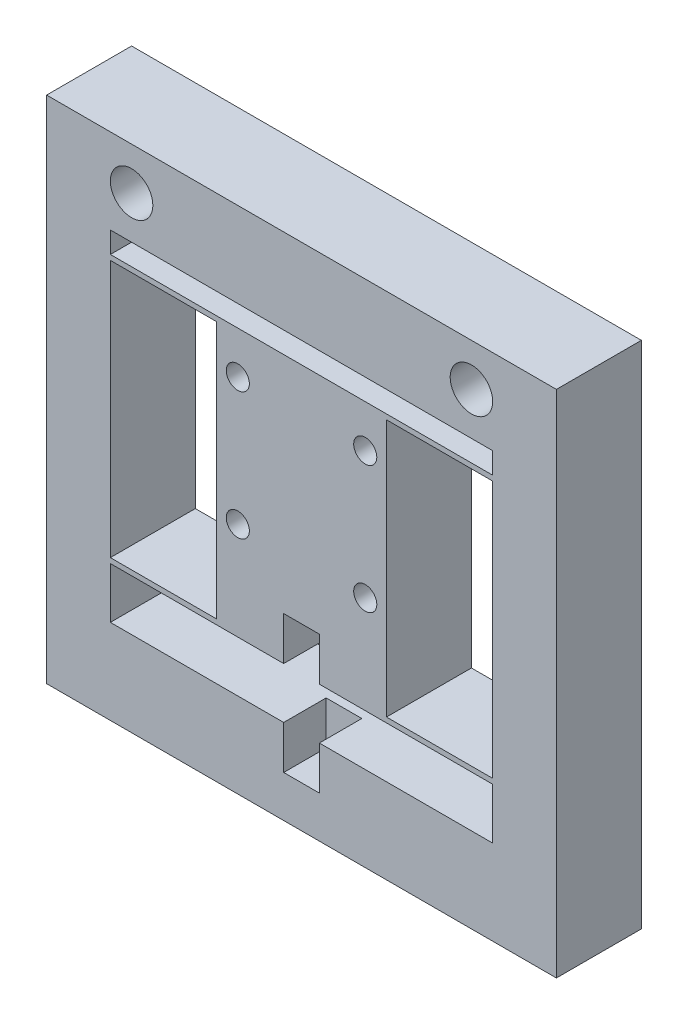
SolidWorks part; units mm, degrees
material "6061 Alloy"
ref_plane "Front Plane" through (0, 0, 0) normal (0, 0, 1) x (1, 0, 0)
ref_plane "Top Plane" through (0, 0, 0) normal (0, 1, 0) x (1, 0, 0)
ref_plane "Right Plane" through (0, 0, 0) normal (1, 0, 0) x (0, 0, -1)
sketch "Sketch1" plane through (0, 0, 0) normal (0, 0, 1) x (1, 0, 0)
  line L1 (-38.1, 38.1) -> (38.1, 38.1)
  line L2 (-38.1, 38.1) -> (-38.1, -38.1)
  line L3 (-38.1, -38.1) -> (38.1, -38.1)
  line L4 (38.1, 38.1) -> (38.1, -38.1)
  dimension "D1" = 38.1
  dimension "D2" = 38.1
  dimension "D3" = 38.1
  dimension "D4" = 38.1
extrude "Boss-Extrude1" add sketch "Sketch1" along normal mid plane 12.7
sketch "Sketch2" plane through (0, 0, 6.35) normal (0, 0, 1) x (1, 0, 0)
  line L0 (38.1, 38.1) -> (-38.1, 38.1) construction
  line L1 (-28.575, 25.4) -> (28.575, 25.4)
  line L2 (-28.575, 25.4) -> (-28.575, 22.225)
  line L3 (-28.575, 22.225) -> (28.575, 22.225)
  line L4 (28.575, 25.4) -> (28.575, 22.225)
  line L5 (12.7, 21.463) -> (28.575, 21.463)
  line L6 (12.7, 21.463) -> (12.7, -17.018)
  line L7 (12.7, -17.018) -> (28.575, -17.018)
  line L8 (28.575, 21.463) -> (28.575, -17.018)
  line L9 (-28.575, 21.463) -> (-12.7, 21.463)
  line L10 (-28.575, 21.463) -> (-28.575, -17.018)
  line L11 (-28.575, -17.018) -> (-12.7, -17.018)
  line L12 (-12.7, 21.463) -> (-12.7, -17.018)
  line L13 (-28.575, -17.78) -> (28.575, -17.78)
  line L14 (-28.575, -17.78) -> (-28.575, -25.4)
  line L15 (-28.575, -25.4) -> (28.575, -25.4)
  line L16 (28.575, -17.78) -> (28.575, -25.4)
  line L17 (38.1, -38.1) -> (38.1, 38.1) construction
  line L18 (-38.1, 38.1) -> (-38.1, -38.1) construction
  line L19 (-38.1, -38.1) -> (38.1, -38.1) construction
  dimension "D1" = 12.7
  dimension "D2" = 9.525
  dimension "D3" = 9.525
  dimension "D4" = 0.762
  dimension "D5" = 0.762
  dimension "D6" = 12.7
  dimension "D7" = 3.175
  dimension "D8" = 7.62
  dimension "D9" = 25.4
  dimension "D10" = 12.7
extrude "Cut-Extrude1" cut sketch "Sketch2" against normal through all
sketch "Sketch3" plane through (0, 0, 6.35) normal (0, 0, 1) x (1, 0, 0)
  line L0 (28.575, -17.78) -> (-28.575, -17.78) construction
  line L1 (-2.667, -11.303) -> (2.667, -11.303)
  line L2 (-2.667, -11.303) -> (-2.667, -31.877)
  line L3 (-2.667, -31.877) -> (2.667, -31.877)
  line L4 (2.667, -11.303) -> (2.667, -31.877)
  line L5 (-28.575, -25.4) -> (28.575, -25.4) construction
  dimension "D1" = 2.667
  dimension "D2" = 2.667
  dimension "D3" = 20.574
  dimension "D4" = 6.477
  dimension "D5" = 6.477
extrude "Cut-Extrude2" cut sketch "Sketch3" against normal blind 6.35
hole_wizard "1/4 (0.25) Diameter Hole1" positions "Sketch5" profile "Sketch4" hole size "1/4" standard "ANSI Inch" end condition up to next
sketch "Sketch5" plane through (0, 0, 6.35) normal (0, 0, 1) x (1, 0, 0)
  line L0 (38.1, 38.1) -> (-38.1, 38.1) construction
  point P0 (-25.4, 31.75)
  point P2 (25.4, 31.75)
  dimension "D1" = 25.4
  dimension "D2" = 25.4
  dimension "D3" = 6.35
sketch "Sketch4" plane through (-25.4, 31.75, 6.35) normal (1, 0, 0) x (0, -1, 0)
  line L0 (0, 0) -> (0, 12.7)
  line L1 (0, 12.7) -> (3.175, 12.7)
  line L2 (3.175, 12.7) -> (3.175, 0)
  line L5 (3.175, 0) -> (0, 0)
  line L11 (0, -6.35) -> (0, 107.95) construction
  dimension "Thru Hole Dia." = 6.35
  dimension "Thru Hole Depth" = 12.7
hole_wizard "#8-32 Tapped Hole1" positions "Sketch7" profile "Sketch6" tap size "#8-32" standard "ANSI Inch" end condition up to next
sketch "Sketch7" plane through (0, 0, 6.35) normal (0, 0, 1) x (1, 0, 0)
  point P0 (-9.525, 15.875)
  point P2 (9.525, 15.875)
  point P4 (9.525, -3.175)
  point P6 (-9.525, -3.175)
  dimension "D1" = 9.525
  dimension "D2" = 9.525
  dimension "D3" = 3.175
  dimension "D4" = 15.875
sketch "Sketch6" plane through (-9.525, 15.875, 6.35) normal (1, 0, 0) x (0, -1, 0)
  line L0 (0, 0) -> (0, 12.7)
  line L1 (0, 12.7) -> (1.7272, 12.7)
  line L2 (1.7272, 12.7) -> (1.7272, 0)
  line L5 (1.7272, 0) -> (0, 0)
  line L11 (0, -6.35) -> (0, 107.95) construction
  dimension "Thru Tap Drill Dia." = 3.4544
  dimension "Thru Tap Drill Depth" = 12.7
cosmetic thread "Hole Thread1" parameters "D2"=4.1656
cosmetic thread "Hole Thread2" parameters "D2"=4.1656
cosmetic thread "Hole Thread3" parameters "D2"=4.1656
cosmetic thread "Hole Thread4" parameters "D2"=4.1656
